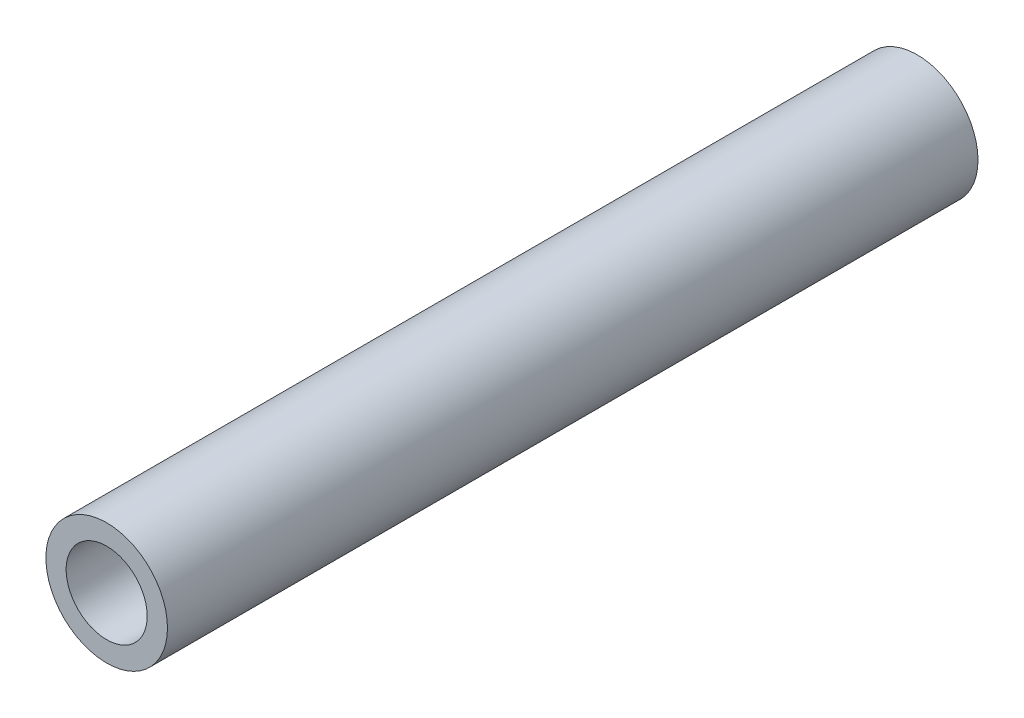
SolidWorks part; units mm, degrees
material "PVC Rigid"
ref_plane "Front Plane" through (0, 0, 0) normal (0, 0, 1) x (1, 0, 0)
ref_plane "Top Plane" through (0, 0, 0) normal (0, 1, 0) x (1, 0, 0)
ref_plane "Right Plane" through (0, 0, 0) normal (1, 0, 0) x (0, 0, -1)
sketch "Sketch1" plane through (0, 0, 0) normal (0, 0, 1) x (1, 0, 0)
  circle A0 centre (0, 0) radius 7.62
  circle A2 centre (0, 0) radius 5.08
  dimension "D1" = 15.24
  dimension "D2" = 10.16
extrude "Boss-Extrude1" add sketch "Sketch1" along normal blind 101.6
